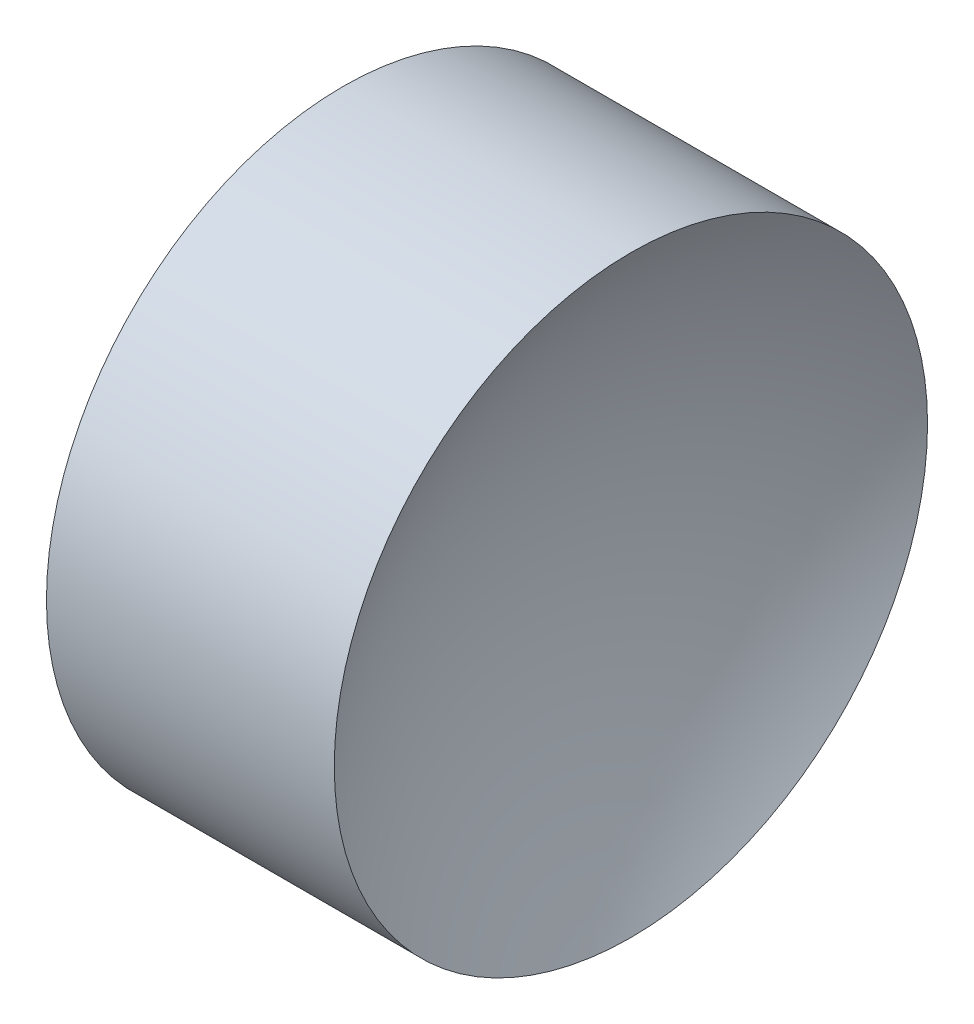
SolidWorks part; units mm, degrees
ref_plane "前视基准面" through (0, 0, 0) normal (0, 0, 1) x (1, 0, 0)
ref_plane "上视基准面" through (0, 0, 0) normal (0, 1, 0) x (1, 0, 0)
ref_plane "右视基准面" through (0, 0, 0) normal (1, 0, 0) x (0, 0, -1)
sketch "草图1" plane through (0, 0, 0) normal (0, 0, 1) x (1, 0, 0)
  line L0 (21.2249, 13.0445) -> (27.8323, 13.0445) construction
  line L1 (23.0243, 13.0445) -> (25.0243, 13.0445)
  line L3 (24.0243, 18.0445) -> (26.45, 18.0445)
  line L4 (24.0243, 18.0445) -> (21.5985, 18.0445)
  arc A0 (23.0243, 13.0445) -> (21.5985, 18.0445) centre (13.5443, 13.0445) ccw
  arc A1 (26.45, 18.0445) -> (25.0243, 13.0445) centre (34.5043, 13.0445) ccw
  dimension "D3" = 9.48
  dimension "D4" = 9.48
  dimension "D1" = 4.8516
  dimension "D2" = 2
revolve "旋转1" add sketch "草图1" angle 360 about L0
